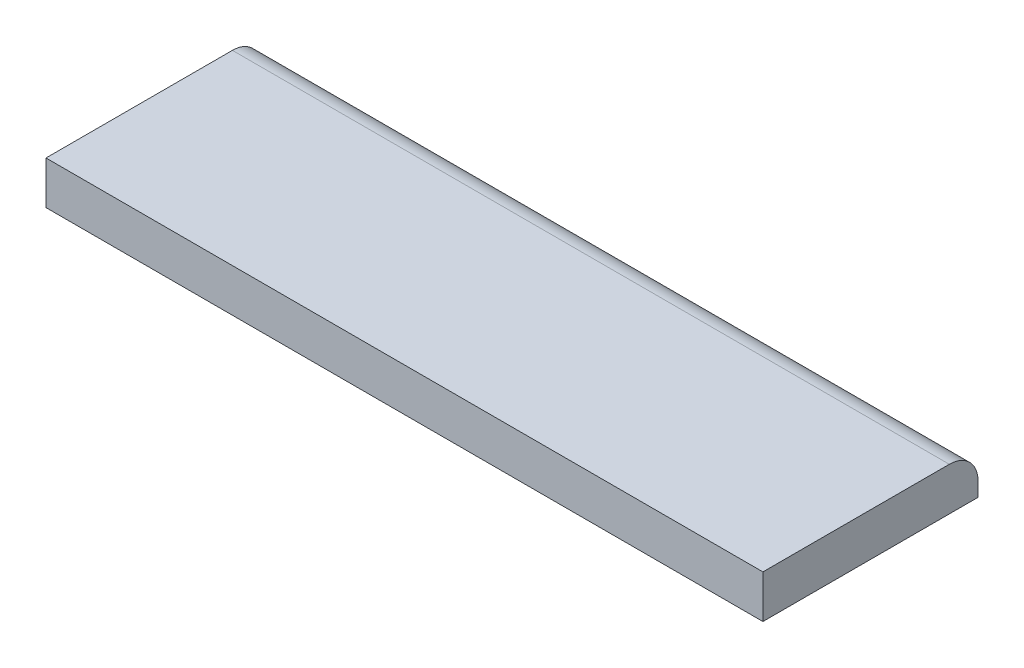
SolidWorks part; units mm, degrees
material "Acrylic (Medium-high impact)"
ref_plane "Front Plane" through (0, 0, 0) normal (0, 0, 1) x (1, 0, 0)
ref_plane "Top Plane" through (0, 0, 0) normal (0, 1, 0) x (1, 0, 0)
ref_plane "Right Plane" through (0, 0, 0) normal (1, 0, 0) x (0, 0, -1)
sketch "Sketch1" plane through (0, 0, 0) normal (0, 1, 0) x (1, 0, 0)
  line L1 (0, 0) -> (50, 0)
  line L2 (0, 0) -> (0, 15)
  line L3 (0, 15) -> (50, 15)
  line L4 (50, 0) -> (50, 15)
  dimension "D1" = 50
  dimension "D2" = 15
extrude "Boss-Extrude1" add sketch "Sketch1" along normal blind 3
fillet "Fillet2" radius 2 1 edges at (25, 3, -15)
